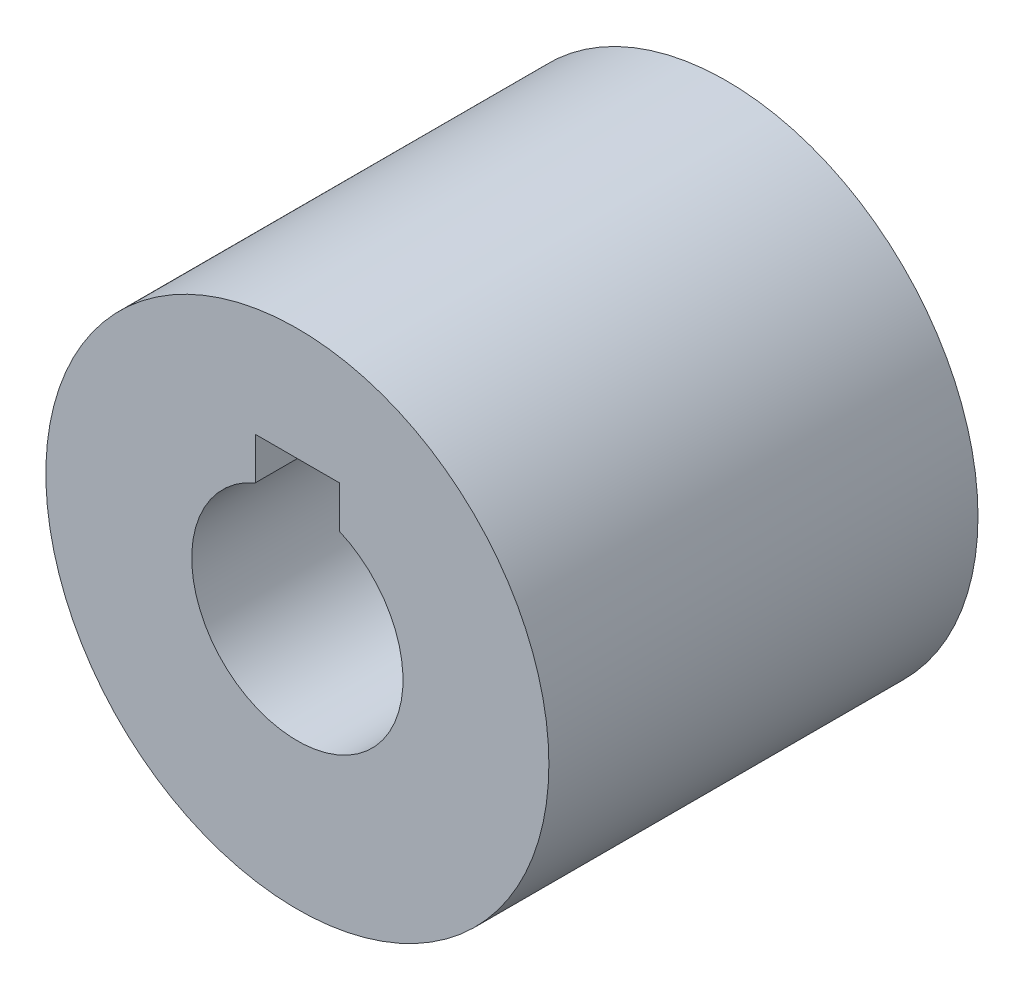
SolidWorks part; units mm, degrees
ref_plane "Front Plane" through (0, 0, 0) normal (0, 0, 1) x (1, 0, 0)
ref_plane "Top Plane" through (0, 0, 0) normal (0, 1, 0) x (1, 0, 0)
ref_plane "Right Plane" through (0, 0, 0) normal (1, 0, 0) x (0, 0, -1)
sketch "Sketch1" plane through (0, 0, 0) normal (0, 0, 1) x (1, 0, 0)
  circle A0 centre (0, 0) radius 9.525
  circle A1 centre (0, 0) radius 4
  dimension "D1" = 8
  dimension "D2" = 19.05
extrude "Boss-Extrude1" add sketch "Sketch1" along normal blind 16.25
sketch "Sketch2" plane through (0, 0, 16.25) normal (0, 0, 1) x (1, 0, 0)
  line L1 (-1.5875, 5.259) -> (1.5875, 5.259)
  line L2 (-1.5875, 5.259) -> (-1.5875, 3.6715)
  line L3 (-1.5875, 3.6715) -> (1.5875, 3.6715)
  line L4 (1.5875, 5.259) -> (1.5875, 3.6715)
  circle A0 centre (0, 0) radius 4 construction
  point P4 (0, 3.6715)
  dimension "D1" = 1.5875
  dimension "D2" = 3.175
extrude "Cut-Extrude1" cut sketch "Sketch2" against normal through all
